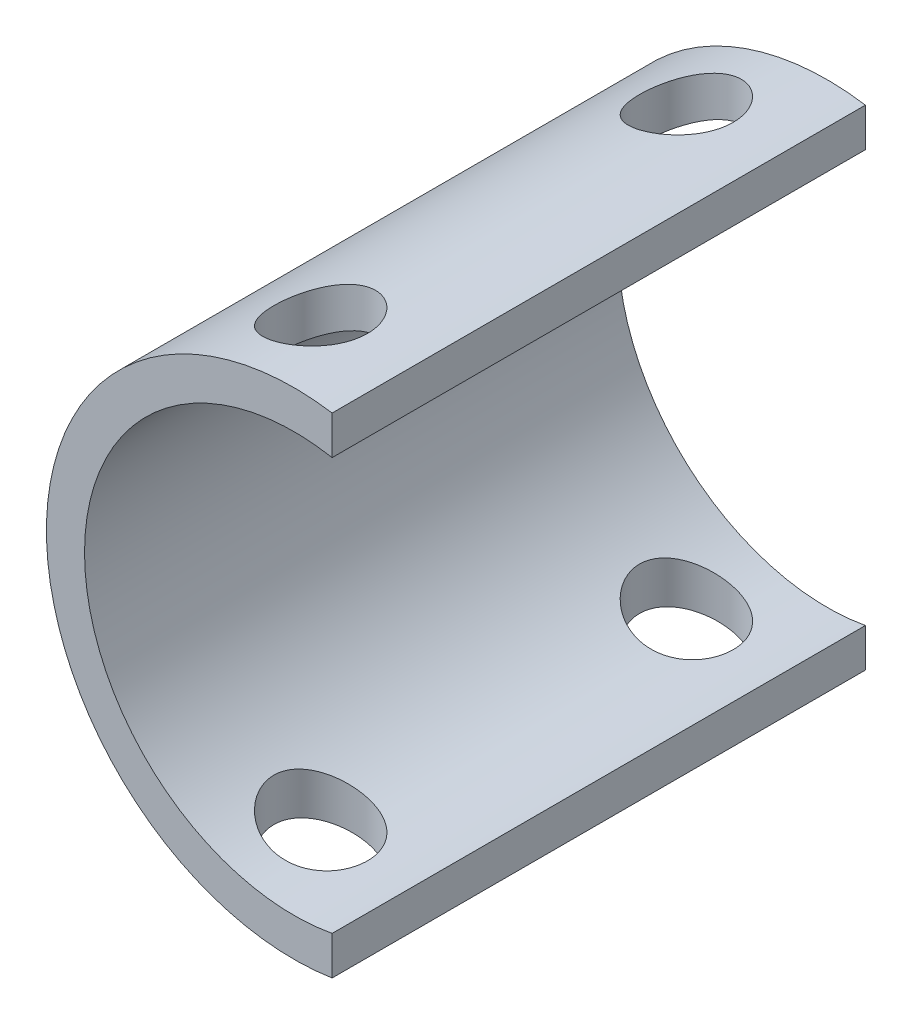
SolidWorks part; units mm, degrees
ref_plane "Plan de face" through (0, 0, 0) normal (0, 0, 1) x (1, 0, 0)
ref_plane "Plan de dessus" through (0, 0, 0) normal (0, 1, 0) x (1, 0, 0)
ref_plane "Plan de droite" through (0, 0, 0) normal (1, 0, 0) x (0, 0, -1)
sketch "Esquisse1" plane through (0, 0, 0) normal (0, 0, 1) x (1, 0, 0)
  circle A0 centre (0, 0) radius 65
  dimension "D1" = 130
ref_plane "Plan1" through (0, 0, 140) normal (0, 0, -1) x (-1, 0, 0)
sketch "Esquisse2" plane through (0, 0, 140) normal (0, 0, -1) x (-1, 0, 0)
  circle A0 centre (0, 0) radius 65
  dimension "D1" = 130
loft "Lissage2" add profiles "Esquisse2", "Esquisse1"
ref_plane "Plan3" through (10, 0, 0) normal (1, 0, 0) x (0, 0, -1)
sketch "Esquisse4" plane through (10, 0, 0) normal (1, 0, 0) x (0, 0, -1)
  line L1 (4.7951, -70.5512) -> (-163.7468, -70.5512)
  line L2 (4.7951, -70.5512) -> (4.7951, 73.0467)
  line L3 (4.7951, 73.0467) -> (-163.7468, 73.0467)
  line L4 (-163.7468, -70.5512) -> (-163.7468, 73.0467)
extrude "Enlèv. mat.-Extru.2" cut sketch "Esquisse4" along normal through all
shell "Coque2" thickness 10
sketch "Esquisse5" plane through (0, 0, 0) normal (0, 0, 1) x (1, 0, 0)
  circle A0 centre (0, 0) radius 55
  dimension "D1" = 110
extrude "Enlèv. mat.-Extru.3" cut sketch "Esquisse5" along normal through all
sketch "Esquisse6" plane through (0, 0, 0) normal (0, 1, 0) x (1, 0, 0)
  line L0 (0, 0) -> (0, -140) construction
  line L1 (66.0001, -140) -> (-66.0001, -140) construction
  line L2 (0, -70) -> (-87.0372, -70) construction
  circle A0 centre (-15, -22) radius 12.2944
  circle A1 centre (-15, -118) radius 12.2944
extrude "Enlèv. mat.-Extru.4" cut sketch "Esquisse6" against normal through all both and the other way through all
